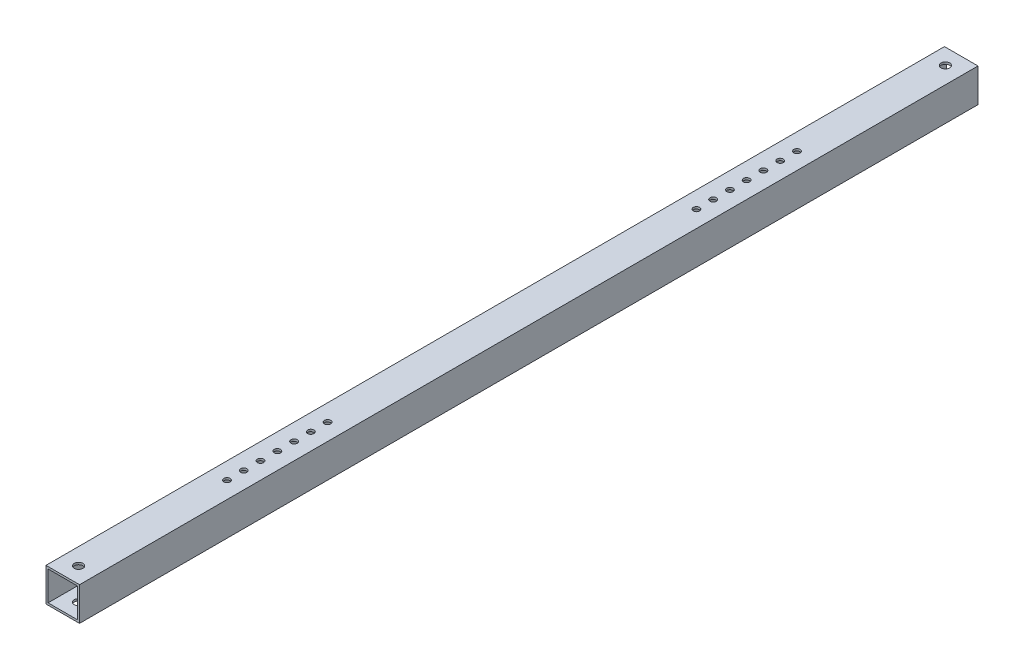
SolidWorks part; units mm, degrees
material "ALUMINUM 6061-T6"
ref_plane "Front Plane" through (0, 0, 0) normal (0, 0, 1) x (1, 0, 0)
ref_plane "Top Plane" through (0, 0, 0) normal (0, 1, 0) x (1, 0, 0)
ref_plane "Right Plane" through (0, 0, 0) normal (1, 0, 0) x (0, 0, -1)
sketch "Sketch1" plane through (0, 0, 0) normal (0, 0, 1) x (1, 0, 0)
  line L1 (-12.7, -12.7) -> (12.7, -12.7)
  line L2 (-12.7, -12.7) -> (-12.7, 12.7)
  line L3 (-12.7, 12.7) -> (12.7, 12.7)
  line L4 (12.7, -12.7) -> (12.7, 12.7)
  line L5 (-12.7, -12.7) -> (12.7, 12.7) construction
  line L6 (-12.7, 12.7) -> (12.7, -12.7) construction
  point P0 (0, 0)
  dimension "D1" = 25.4
  dimension "D2" = 25.4
extrude "Boss-Extrude1" add sketch "Sketch1" along normal mid plane 680.72
sketch "Sketch2" plane through (0, 0, 340.36) normal (0, 0, 1) x (1, 0, 0)
  line L0 (-11.1125, 11.1125) -> (-11.1125, -11.1125)
  line L1 (-12.7, 12.7) -> (12.7, 12.7)
  line L2 (-12.7, 12.7) -> (-12.7, -12.7)
  line L3 (-12.7, -12.7) -> (12.7, -12.7)
  line L4 (12.7, 12.7) -> (12.7, -12.7)
  line L5 (-11.1125, -11.1125) -> (11.1125, -11.1125)
  line L6 (11.1125, 11.1125) -> (11.1125, -11.1125)
  line L7 (-11.1125, 11.1125) -> (11.1125, 11.1125)
  dimension "D1" = 1.5875
extrude "Cut-Extrude1" cut sketch "Sketch2" against normal through all contours L7 L6 L5 L0
sketch "Sketch3" plane through (0, 12.7, 0) normal (0, 1, 0) x (1, 0, 0)
  line L1 (-12.7, -340.36) -> (-12.7, 340.36) construction
  circle A0 centre (0, -215.9) radius 2.3812
  circle A1 centre (0, -203.2) radius 2.3812
  circle A2 centre (0, -190.5) radius 2.3812
  circle A3 centre (0, -177.8) radius 2.3812
  circle A4 centre (0, -165.1) radius 2.3812
  circle A5 centre (0, -152.4) radius 2.3812
  circle A6 centre (0, -139.7) radius 2.3812
  circle A7 centre (0, 139.7) radius 2.3812
  circle A8 centre (0, 152.4) radius 2.3812
  circle A9 centre (0, 165.1) radius 2.3812
  circle A10 centre (0, 177.8) radius 2.3812
  circle A11 centre (0, 190.5) radius 2.3812
  circle A12 centre (0, 215.9) radius 2.3813
  circle A13 centre (0, 203.2) radius 2.3812
  point P29 (0, 177.8)
  point P32 (-12.7, 0)
  point P33 (0, -177.8)
  dimension "D1" = 4.7625
  dimension "D2" = 12.7
  dimension "D3" = 12.7
  dimension "D4" = 12.7
  dimension "D5" = 12.7
  dimension "D6" = 12.7
  dimension "D7" = 12.7
  dimension "D8" = 4.7625
  dimension "D9" = 12.7
  dimension "D10" = 12.7
  dimension "D12" = 12.7
  dimension "D13" = 12.7
  dimension "D14" = 12.7
  dimension "D16" = 177.8
  dimension "D11" = 12.7
  dimension "D15" = 355.6
extrude "Cut-Extrude2" cut sketch "Sketch3" against normal through all
sketch3d "3DSketch1"
hole_wizard "M6 Clearance Hole1" positions "Sketch5" profile "Sketch4" hole size "M6" standard "ANSI Metric" end condition through all
sketch "Sketch5" plane through (0, 12.7, 0) normal (0, 1, 0) x (1, 0, 0)
  line L0 (-11.1125, 340.36) -> (11.1125, 340.36) construction
  line L1 (12.7, -340.36) -> (-12.7, -340.36) construction
  point P0 (0, 328.36)
  point P2 (0, -328.36)
  point P5 (0, 340.36)
  dimension "D1" = 12
  dimension "D2" = 12
sketch "Sketch4" plane through (0, 12.7, -328.36) normal (1, 0, 0) x (0, 0, 1)
  line L0 (0, 0) -> (0, 25.4)
  line L1 (0, 25.4) -> (3.3, 25.4)
  line L2 (3.3, 25.4) -> (3.3, 0)
  line L5 (3.3, 0) -> (0, 0)
  line L11 (0, -6.35) -> (0, 107.95) construction
  dimension "Thru Hole Dia." = 6.6
  dimension "Thru Hole Depth" = 25.4
